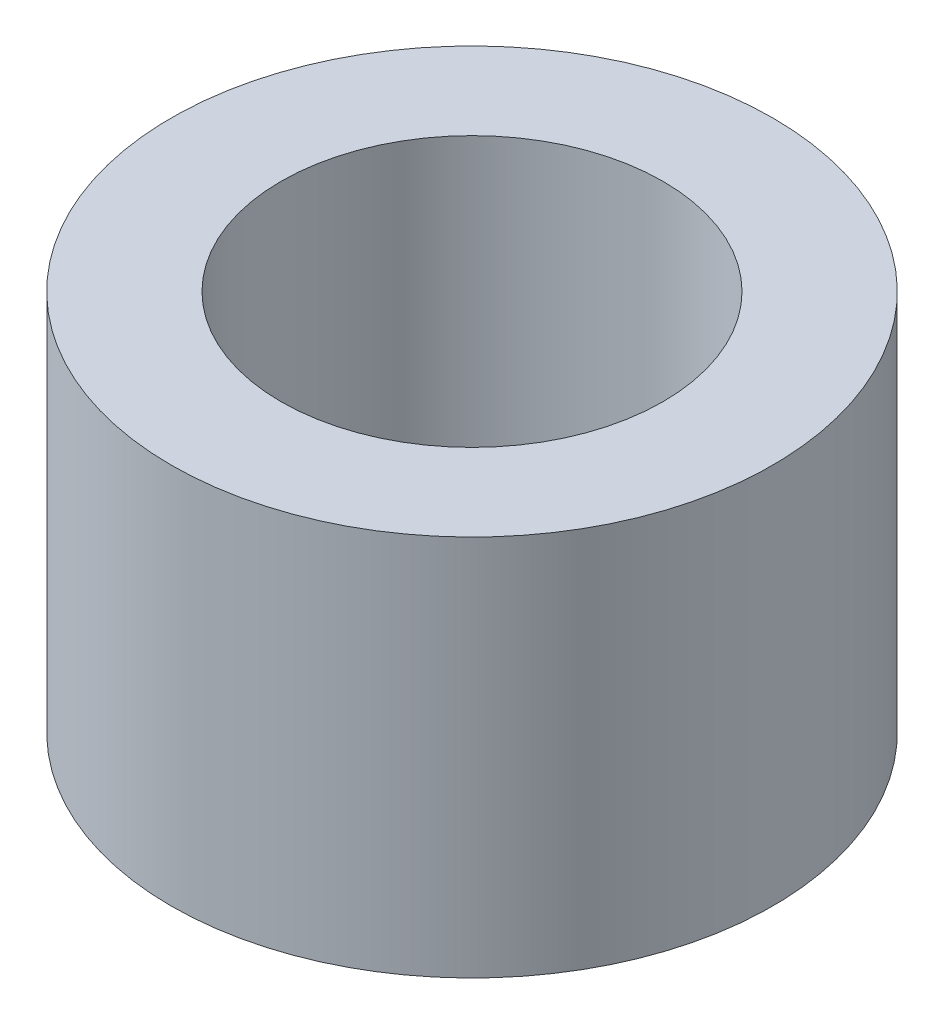
SolidWorks part; units mm, degrees
material "Brass"
ref_plane "Front Plane" through (0, 0, 0) normal (0, 0, 1) x (1, 0, 0)
ref_plane "Top Plane" through (0, 0, 0) normal (0, 1, 0) x (1, 0, 0)
ref_plane "Right Plane" through (0, 0, 0) normal (1, 0, 0) x (0, 0, -1)
sketch "Sketch1" plane through (0, 0, 0) normal (0, 0, 1) x (1, 0, 0)
  line L0 (0, 0) -> (0, 4) construction
  line L2 (2, 4) -> (2, 0)
  line L4 (2, 4) -> (3.15, 4)
  line L5 (3.15, 4) -> (3.15, 0)
  line L7 (3.15, 0) -> (2, 0)
  dimension "D1" = 4
  dimension "D2" = 2
  dimension "D3" = 3.15
revolve "Revolve1" add sketch "Sketch1" angle 360 about L0
move or copy body "Body-Move/Copy1" bodies to move or copy 101 parameters "D1"=0, "D2"=0, "D3"=0
